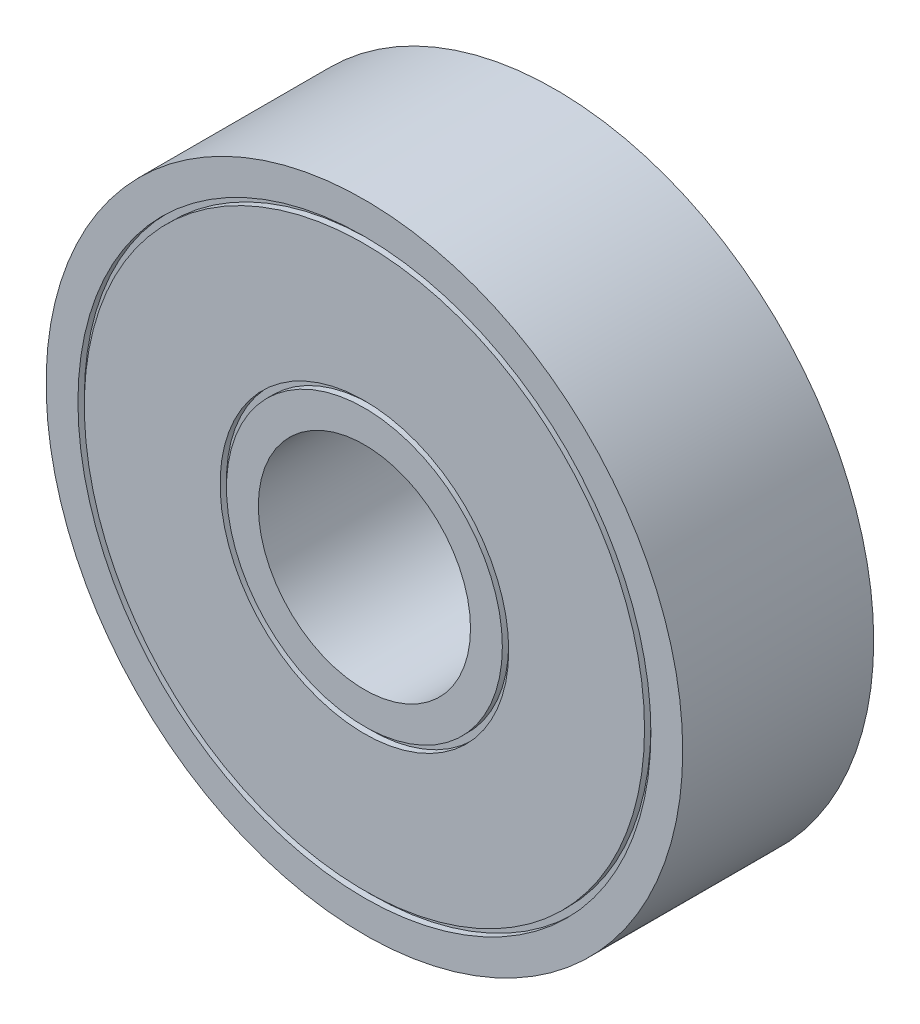
SolidWorks part; units mm, degrees
ref_plane "Alzado" through (0, 0, 0) normal (0, 0, 1) x (1, 0, 0)
ref_plane "Planta" through (0, 0, 0) normal (0, 1, 0) x (1, 0, 0)
ref_plane "Vista lateral" through (0, 0, 0) normal (1, 0, 0) x (0, 0, -1)
sketch "Croquis1" plane through (0, 0, 0) normal (0, 0, 1) x (1, 0, 0)
  circle A0 centre (0, 0) radius 15
  circle A1 centre (0, 0) radius 5
  dimension "D1" = 30
  dimension "D2" = 10
extrude "Saliente-Extruir1" add sketch "Croquis1" along normal blind 9
sketch "Croquis2" plane through (0, 0, 9) normal (0, 0, 1) x (1, 0, 0)
  circle A2 centre (0, 0) radius 13.5
  circle A3 centre (0, 0) radius 13.5
  circle A4 centre (0, 0) radius 13.2
  circle A5 centre (0, 0) radius 6.5
  circle A6 centre (0, 0) radius 6.5
  circle A7 centre (0, 0) radius 6.8
  dimension "D1" = 1.5
  dimension "D2" = 1.5
  dimension "D3" = 0.3
  dimension "D4" = 0.3
extrude "Cortar-Extruir1" cut sketch "Croquis2" against normal blind 0.3 contours A3 A4 | A7 A6
ref_plane "Plano1" through (0, 0, 4.5) normal (0, 0, 1) x (1, 0, 0)
mirror "Simetría1" about plane through (0, 0, 4.5) normal (0, 0, 1) of "Cortar-Extruir1"
